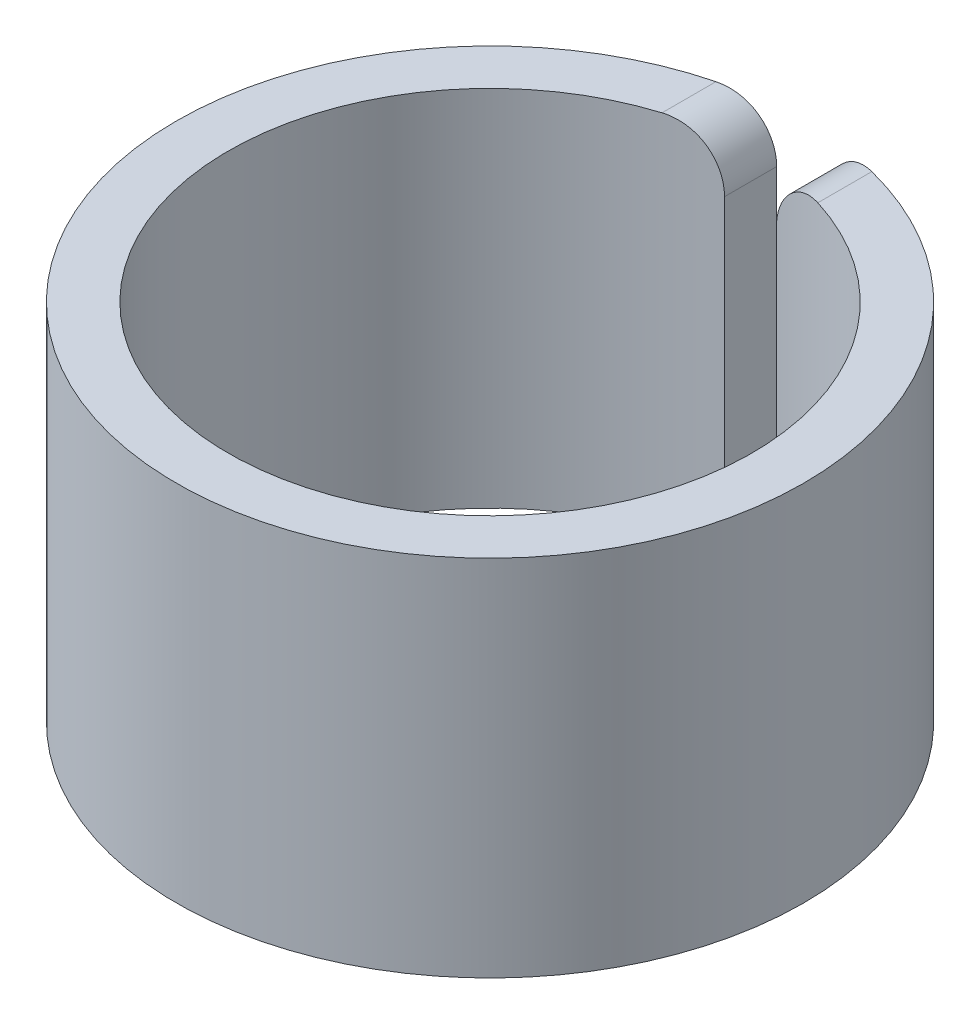
SolidWorks part; units mm, degrees
ref_plane "Front Plane" through (0, 0, 0) normal (0, 0, 1) x (1, 0, 0)
ref_plane "Top Plane" through (0, 0, 0) normal (0, 1, 0) x (1, 0, 0)
ref_plane "Right Plane" through (0, 0, 0) normal (1, 0, 0) x (0, 0, -1)
sketch "Sketch3" plane through (0, 0, 0) normal (0, 1, 0) x (1, 0, 0)
  circle A0 centre (0, 0) radius 5.04
  point P4 (0, 0)
  point P5 (0.3031, 9.02)
  dimension "D1" = 10.08
extrude "Extrude-Thin1" add sketch "Sketch3" along normal mid plane 7 thin
sketch "Sketch4" plane through (0, 0, 0) normal (0, 1, 0) x (1, 0, 0)
  line L5 (0.5, 0) -> (-0.5, 0)
  line L6 (0.5, 0) -> (0.5, 1000)
  line L7 (0.5, 1000) -> (-0.5, 1000)
  line L8 (-0.5, 0) -> (-0.5, 1000)
  circle A1 centre (0, 0) radius 6.04 construction
  point P4 (0, 0)
  dimension "D1" = 1
  dimension "D2" = 1000
extrude "Cut-Extrude1" cut sketch "Sketch4" against normal through all both and the other way through all
fillet "Fillet1" radius 1 4 edges at (0.5, 3.5, -5.5172) (-0.5, 3.5, -5.5172) (-0.5, -3.5, -5.5172) (0.5, -3.5, -5.5172)
